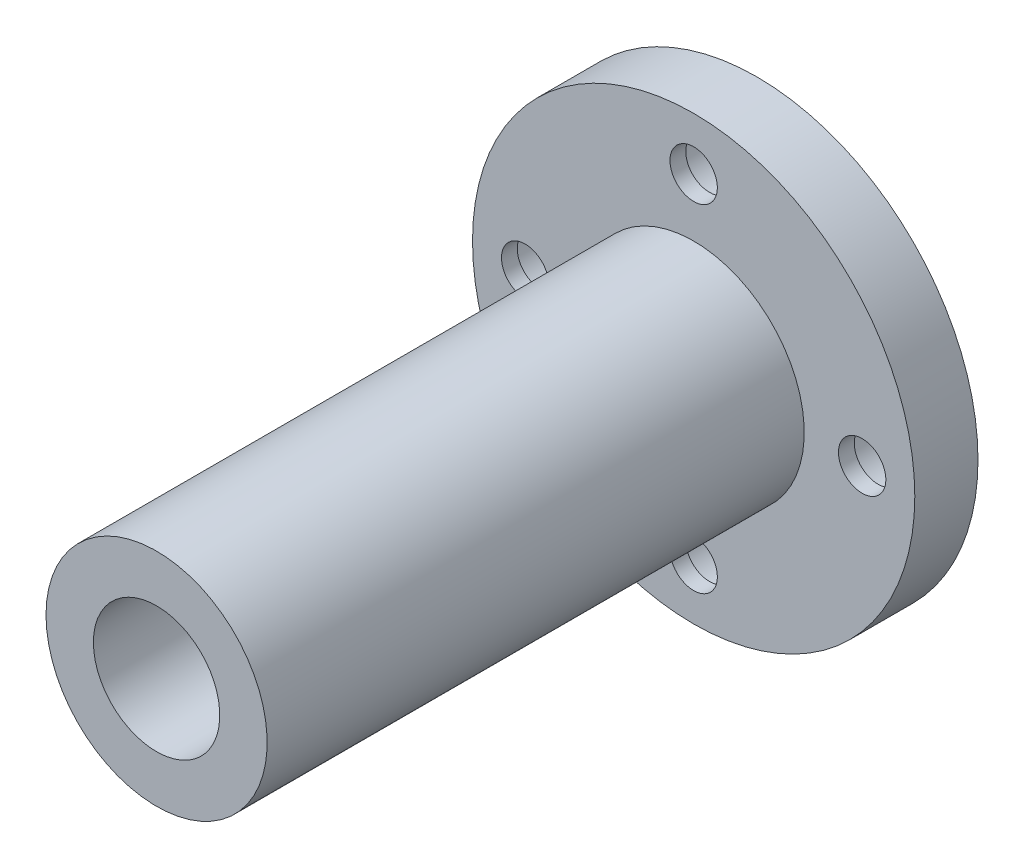
SolidWorks part; units mm, degrees
material "acero"
ref_plane "Alzado" through (0, 0, 0) normal (0, 0, 1) x (1, 0, 0)
ref_plane "Planta" through (0, 0, 0) normal (0, 1, 0) x (1, 0, 0)
ref_plane "Vista lateral" through (0, 0, 0) normal (1, 0, 0) x (0, 0, -1)
sketch "Croquis5" plane through (0, 0, 0) normal (1, 0, 0) x (0, 0, -1)
  line L0 (0, 0) -> (-89.5005, 0) construction
  line L1 (0, 6) -> (-57, 6)
  line L2 (-57, 6) -> (-57, 10.5)
  line L3 (-57, 10.5) -> (-6, 10.5)
  line L4 (-6, 10.5) -> (-6, 21)
  line L5 (-6, 21) -> (0, 21)
  line L6 (0, 21) -> (0, 6)
  dimension "D1" = 6
  dimension "D2" = 10.5
  dimension "D3" = 21
  dimension "D4" = 6
  dimension "D5" = 51
revolve "Revolución1" add sketch "Croquis5" angle 360 about L0
sketch "Croquis6" plane through (0, 0, 6) normal (0, 0, 1) x (1, 0, 0)
  line L0 (0, 0) -> (0, 16) construction
  circle A0 centre (0, 16) radius 2.25
  circle A1 centre (16, 0) radius 2.25
  circle A2 centre (0, -16) radius 2.25
  circle A3 centre (-16, 0) radius 2.25
  point P13 (0, 0)
  dimension "D2" = 4.5
  dimension "D1" = 16
  dimension "D3" = 4
extrude "Cortar-Extruir3" cut sketch "Croquis6" against normal through all
sketch "Croquis7" plane through (0, 0, 0) normal (0, 0, -1) x (-1, 0, 0)
  line L0 (0, 0) -> (0, 16) construction
  circle A0 centre (0, 16) radius 3.75
  circle A1 centre (16, 0) radius 3.75
  circle A2 centre (0, -16) radius 3.75
  circle A3 centre (-16, 0) radius 3.75
  point P14 (0, 0)
  dimension "D1" = 7.5
  dimension "D2" = 4
extrude "Cortar-Extruir4" cut sketch "Croquis7" against normal blind 4.5
